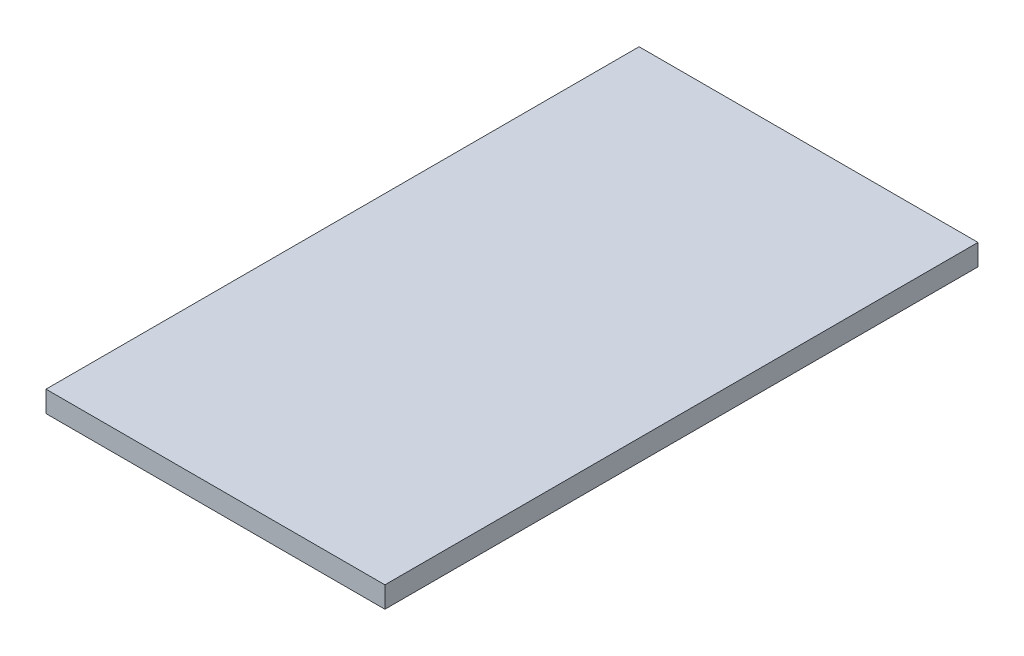
SolidWorks part; units mm, degrees
material "Glass"
ref_plane "Front Plane" through (0, 0, 0) normal (0, 0, 1) x (1, 0, 0)
ref_plane "Top Plane" through (0, 0, 0) normal (0, 1, 0) x (1, 0, 0)
ref_plane "Right Plane" through (0, 0, 0) normal (1, 0, 0) x (0, 0, -1)
sketch "Sketch1" plane through (0, 0, 0) normal (0, 1, 0) x (1, 0, 0)
  line L1 (-24, 42) -> (24, 42)
  line L2 (-24, 42) -> (-24, -42)
  line L3 (-24, -42) -> (24, -42)
  line L4 (24, 42) -> (24, -42)
  line L5 (-24, 42) -> (24, -42) construction
  line L6 (-24, -42) -> (24, 42) construction
  point P0 (0, 0)
  dimension "D1" = 48
  dimension "D2" = 84
extrude "Boss-Extrude1" add sketch "Sketch1" along normal blind 3
